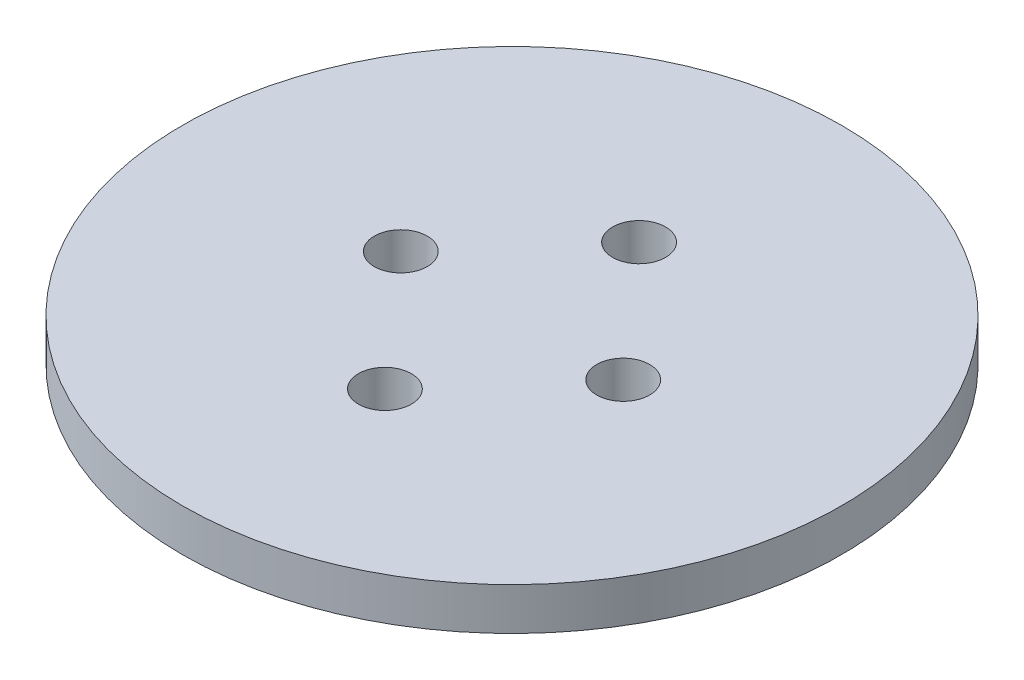
SolidWorks part; units mm, degrees
material "Pine"
ref_plane "Front Plane" through (0, 0, 0) normal (0, 0, 1) x (1, 0, 0)
ref_plane "Top Plane" through (0, 0, 0) normal (0, 1, 0) x (1, 0, 0)
ref_plane "Right Plane" through (0, 0, 0) normal (1, 0, 0) x (0, 0, -1)
sketch "Sketch1" plane through (0, 0, 0) normal (0, 1, 0) x (1, 0, 0)
  circle A0 centre (0, 0) radius 49.403
  dimension "D1" = 98.806
extrude "Boss-Extrude1" add sketch "Sketch1" along normal blind 6.35
hole_wizard "Threaded Rod Holes" positions "Sketch2" profile "Sketch3" tap size "5/16-18" standard "ANSI Inch" end condition through all
sketch "Sketch2" plane through (0, 6.35, 0) normal (0, 1, 0) x (1, 0, 0)
  line L0 (0, 19.05) -> (0, 0) construction
  line L1 (0, 0) -> (0, -19.05) construction
  point P16 (0, 19.05)
  point P23 (0, -19.05)
  dimension "D1" = 38.1
sketch "Sketch3" plane through (0, 6.35, -19.05) normal (1, 0, 0) x (0, 0, 1)
  line L0 (0, 0) -> (0, 6.35)
  line L1 (0, 6.35) -> (3.9687, 6.35)
  line L2 (3.9687, 6.35) -> (3.9687, 0)
  line L5 (3.9687, 0) -> (0, 0)
  line L11 (0, -6.35) -> (0, 107.95) construction
  dimension "Thru Tap Drill Dia." = 7.9375
  dimension "Thru Tap Drill Depth" = 6.35
cosmetic thread "Hole Thread1" parameters "D2"=7.9375
cosmetic thread "Hole Thread2" parameters "D2"=7.9375
hole_wizard "U-Bolt Holes" positions "Sketch4" profile "Sketch5" tap size "5/16-18" standard "ANSI Inch" end condition through all
sketch "Sketch4" plane through (0, 6.35, 0) normal (0, 1, 0) x (1, 0, 0)
  line L0 (0, 0) -> (0, 14.8177) construction
  point P0 (-16.6687, 0)
  point P10 (16.6687, 0)
  dimension "D1" = 33.3375
sketch "Sketch5" plane through (-16.6687, 6.35, 0) normal (1, 0, 0) x (0, 0, 1)
  line L0 (0, 0) -> (0, 6.35)
  line L1 (0, 6.35) -> (3.9687, 6.35)
  line L2 (3.9687, 6.35) -> (3.9687, 0)
  line L5 (3.9687, 0) -> (0, 0)
  line L11 (0, -6.35) -> (0, 107.95) construction
  dimension "Thru Tap Drill Dia." = 7.9375
  dimension "Thru Tap Drill Depth" = 6.35
cosmetic thread "Hole Thread3" parameters "D2"=7.9375
cosmetic thread "Hole Thread4" parameters "D2"=7.9375
